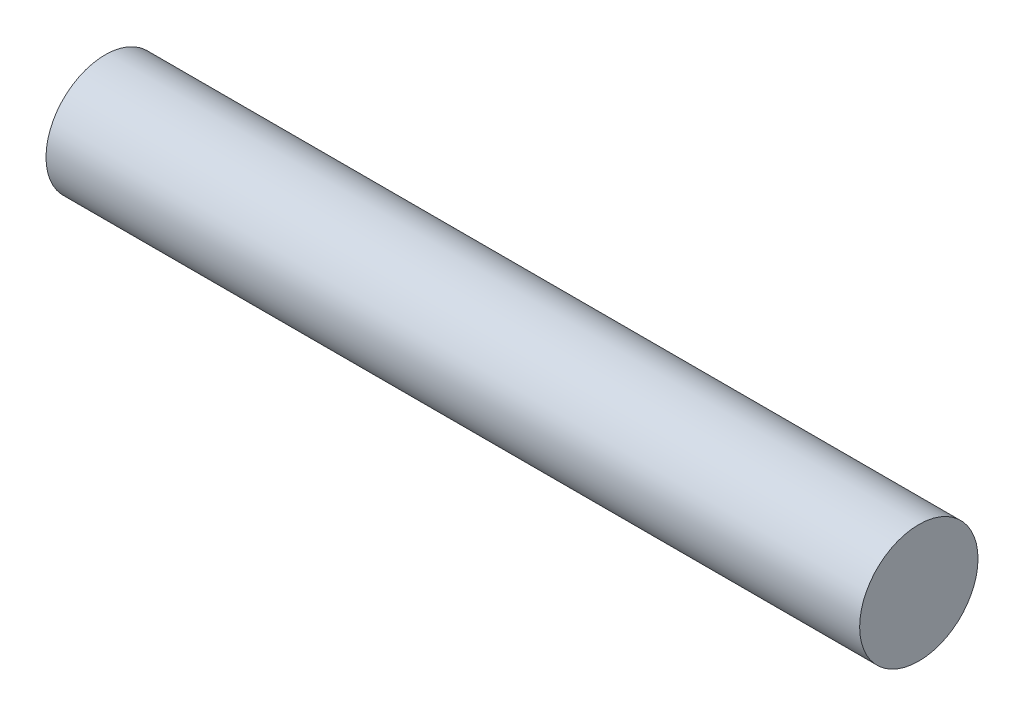
SolidWorks part; units mm, degrees
ref_plane "Front Plane" through (0, 0, 0) normal (0, 0, 1) x (1, 0, 0)
ref_plane "Top Plane" through (0, 0, 0) normal (0, 1, 0) x (1, 0, 0)
ref_plane "Right Plane" through (0, 0, 0) normal (1, 0, 0) x (0, 0, -1)
sketch "Sketch1" plane through (0, 0, 0) normal (1, 0, 0) x (0, 0, -1)
  circle A0 centre (0, 0) radius 3
  dimension "D1" = 6
extrude "Boss-Extrude1" add sketch "Sketch1" along normal blind 36.75
sketch "Sketch3" plane through (0, 0, 0) normal (-1, 0, 0) x (0, 0, 1)
  circle A0 centre (0, 0) radius 3
extrude "Boss-Extrude2" add sketch "Sketch3" along normal blind 4.5
